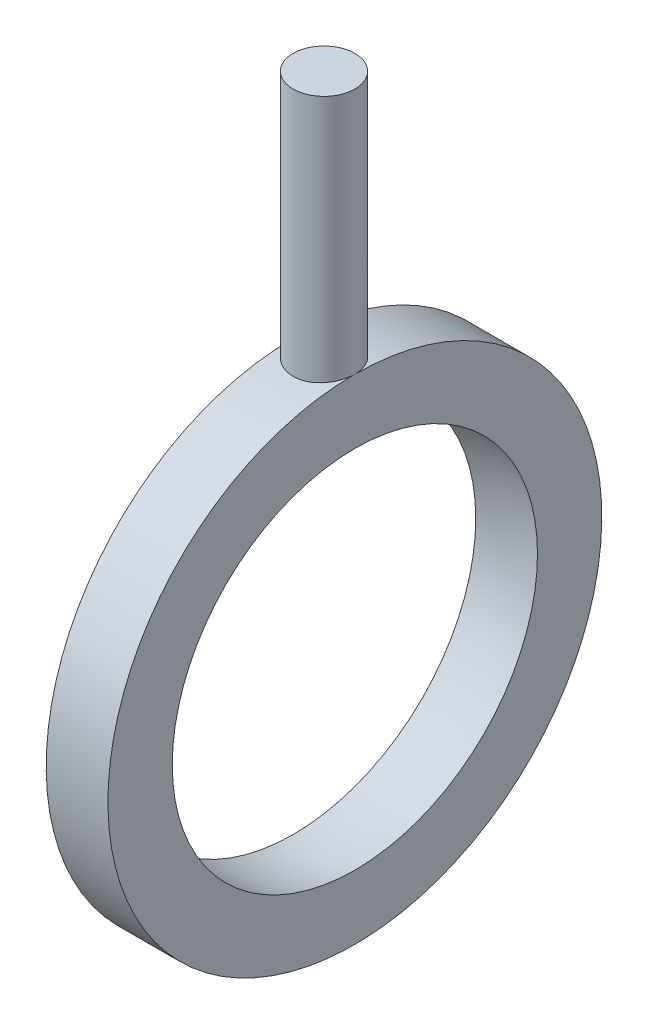
SolidWorks part; units mm, degrees
ref_plane "Front Plane" through (0, 0, 0) normal (0, 0, 1) x (1, 0, 0)
ref_plane "Top Plane" through (0, 0, 0) normal (0, 1, 0) x (1, 0, 0)
ref_plane "Right Plane" through (0, 0, 0) normal (1, 0, 0) x (0, 0, -1)
sketch "Sketch1" plane through (0, 0, 0) normal (0, 0, 1) x (1, 0, 0)
  line L0 (0, 0) -> (0, 20) construction
  line L1 (0, 20) -> (6.642, 20) construction
  line L2 (-2.5, 20) -> (2.5, 20)
  line L3 (2.5, 20) -> (2.5, 10.3308) construction
  line L4 (2.5, 10.3308) -> (-2.5, 10.3308) construction
  line L5 (-2.5, 10.3308) -> (-2.5, 20) construction
  line L6 (-2.5, 20) -> (-2.5, 14.7902)
  line L7 (2.5, 20) -> (2.5, 14.7902)
  line L8 (0, 0) -> (15, 0) construction
  circle A2 centre (0, 0) radius 15 construction
  arc A3 (-2.5, 14.7902) -> (2.5, 14.7902) centre (0, 0) cw
  point P8 (0, 20)
  dimension "D1" = 20
  dimension "D2" = 5
revolve "Revolve1" add sketch "Sketch1" angle 360 about L8
ref_plane "Plane1" through (0, 40, 0) normal (0, 1, 0) x (1, 0, 0)
sketch "Sketch3" plane through (0, 40, 0) normal (0, 1, 0) x (1, 0, 0)
  circle A0 centre (0, 0) radius 2.5
extrude "Boss-Extrude2" add sketch "Sketch3" against normal up to surface (20.1569 mm away)
